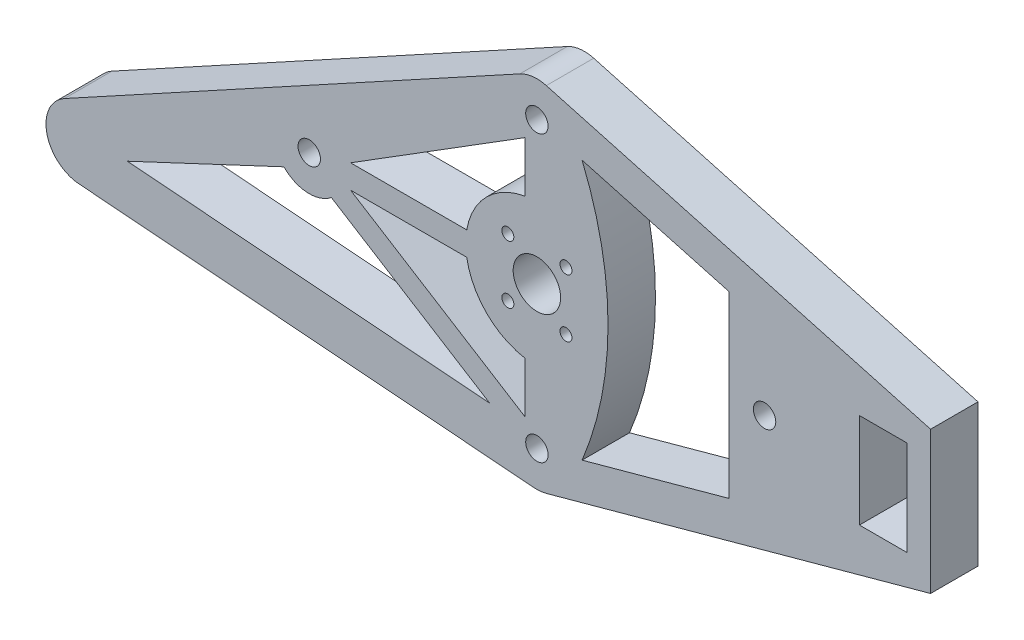
SolidWorks part; units mm, degrees
ref_plane "Front Plane" through (0, 0, 0) normal (0, 0, 1) x (1, 0, 0)
ref_plane "Top Plane" through (0, 0, 0) normal (0, 1, 0) x (1, 0, 0)
ref_plane "Right Plane" through (0, 0, 0) normal (1, 0, 0) x (0, 0, -1)
sketch "Sketch1" plane through (0, 0, 0) normal (0, 0, 1) x (1, 0, 0)
  line L0 (-3.8891, 3.8891) -> (3.8891, -3.8891) construction
  line L1 (0, -55) -> (0, 55) construction
  line L2 (-3.8891, -3.8891) -> (3.8891, 3.8891) construction
  line L3 (-1000, 0) -> (49000, 0) construction
  line L4 (-969.52, -25.4) -> (49030.48, -25.4) construction
  line L5 (40.005, 9.525) -> (52.705, 9.525) construction
  line L6 (43.18, 6.35) -> (49.53, 6.35)
  line L7 (43.18, 6.35) -> (43.18, -6.35)
  line L8 (43.18, -6.35) -> (49.53, -6.35)
  line L9 (49.53, 6.35) -> (49.53, -6.35)
  line L10 (43.18, 6.35) -> (49.53, -6.35) construction
  line L11 (43.18, -6.35) -> (49.53, 6.35) construction
  line L12 (52.705, 9.525) -> (52.705, -9.525)
  line L13 (40.005, -9.525) -> (52.705, -9.525) construction
  line L14 (40.005, 0) -> (40.005, -9.525) construction
  line L15 (55, 0) -> (-55, 0) construction
  line L16 (52.705, -9.525) -> (1.2604, -23.6427)
  line L17 (52.705, 9.525) -> (1.2604, 23.6427)
  line L18 (-61.3309, -19.0355) -> (-0.3709, -23.798)
  line L20 (-2.2851, 23.2285) -> (-63.2451, -10.109)
  line L21 (40.005, 9.525) -> (40.005, 0) construction
  line L22 (40.005, 9.525) -> (40.005, -9.525) construction
  line L23 (-63.2451, -10.109) -> (-91.2058, -25.4) construction
  circle A0 centre (0, 0) radius 3.175
  circle A1 centre (-3.8891, 3.8891) radius 0.8
  circle A2 centre (3.8891, -3.8891) radius 0.8
  circle A3 centre (30.48, 0) radius 1.5
  circle A4 centre (-30.48, 0) radius 1.5
  circle A5 centre (3.8891, 3.8891) radius 0.8
  circle A6 centre (-3.8891, -3.8891) radius 0.8
  circle A7 centre (30.48, 0) radius 25.4 construction
  circle A8 centre (-30.48, 0) radius 25.4 construction
  circle A9 centre (-60.96, -14.2875) radius 1.5 construction
  arc A10 (-63.2451, -10.109) -> (-61.3309, -19.0355) centre (-60.96, -14.2875) ccw
  circle A11 centre (0, -19.05) radius 1.5
  arc A12 (-0.3709, -23.798) -> (1.2604, -23.6427) centre (0, -19.05) ccw
  circle A13 centre (0, 19.05) radius 1.5
  arc A14 (-2.2851, 23.2285) -> (1.2604, 23.6427) centre (0, 19.05) cw
  arc A16 (-61.3309, -19.0355) -> (-63.2451, -10.109) centre (-60.96, -14.2875) ccw construction
  circle A17 centre (-28.8925, 15.875) radius 38.1 construction
  arc A20 (1.2604, 23.6427) -> (-2.2851, 23.2285) centre (0, 19.05) cw construction
  arc A21 (1.2604, -23.6427) -> (-0.3709, -23.798) centre (0, -19.05) ccw construction
  point P6 (0, 0)
  point P17 (0, 0)
  point P32 (0, -23.8125)
  point P33 (46.355, 0)
  point P50 (-92.3925, -25.4)
  point P51 (-28.8925, -22.225)
  point P52 (-66.9925, 15.875)
  point P57 (-51.8715, -3.8891)
  dimension "D1" = 6.35
  dimension "D3" = 3
  dimension "D4" = 1.6
  dimension "D7" = 50.8
  dimension "D10" = 9.525
  dimension "D11" = 1.5875
  dimension "D16" = 1.5875
  dimension "D18" = 76.2
  dimension "D2" = 11
  dimension "D5" = 45
  dimension "D6" = 30.48
  dimension "D8" = 11.1125
  dimension "D9" = 30.48
  dimension "D12" = 6.35
  dimension "D13" = 12.7
  dimension "D15" = 15.875
  dimension "D17" = 3.175
  dimension "D19" = 25.4
  dimension "D20" = 44.8319
  dimension "D14" = 3.175
extrude "Boss-Extrude1" add sketch "Sketch1" along normal mid plane 6.35
sketch "Sketch2" plane through (0, 0, 3.175) normal (0, 0, 1) x (1, 0, 0)
  line L0 (-60.96, -14.2875) -> (-30.48, 0) construction
  line L1 (-30.48, 0) -> (0, -19.05) construction
  line L2 (0, -19.05) -> (-60.96, -14.2875) construction
  line L3 (-6.3349, -16.9627) -> (-54.8423, -13.1731)
  line L4 (-54.8423, -13.1731) -> (-33.8718, -3.3432)
  line L5 (-27.5138, -3.726) -> (-6.3349, -16.9627)
  line L6 (-30.5886, -1.8042) -> (-27.5138, -3.726) construction
  line L7 (-30.5886, -1.8042) -> (-6.3349, -16.9627) construction
  line L8 (-33.8718, -3.3432) -> (-30.5886, -1.8042) construction
  line L9 (-54.8423, -13.1731) -> (-30.5886, -1.8042) construction
  line L10 (25.7175, 11.9925) -> (25.7175, -11.9925)
  line L11 (25.7175, 11.9925) -> (6.0495, 17.3899)
  line L12 (52.705, 9.525) -> (1.2604, 23.6427) construction
  line L13 (25.7175, -11.9925) -> (6.0495, -17.3899)
  line L14 (1.2604, -23.6427) -> (52.705, -9.525) construction
  arc A0 (-33.8718, -3.3432) -> (-27.5138, -3.726) centre (-30.48, 0) ccw
  circle A1 centre (0, -19.05) radius 4.7625 construction
  circle A2 centre (-60.96, -14.2875) radius 4.7625 construction
  circle A3 centre (0, 0) radius 9.525 construction
  circle A4 centre (0, 19.05) radius 4.7625 construction
  circle A5 centre (30.48, 0) radius 4.7625 construction
  arc A6 (-26.4414, -2.5241) -> (-34.7922, -2.0214) centre (-30.48, 0) ccw construction
  arc A7 (-34.7922, -2.0214) -> (-33.8718, -3.3432) centre (-30.48, 0) ccw construction
  arc A8 (-27.5138, -3.726) -> (-26.4414, -2.5241) centre (-30.48, 0) ccw construction
  arc A9 (6.0495, 17.3899) -> (6.0495, -17.3899) centre (-35.7188, 0) cw
  arc A10 (4.2022, 21.2912) -> (6.0495, 17.3899) centre (-35.7188, 0) cw construction
  arc A11 (6.0495, -17.3899) -> (4.2022, -21.2912) centre (-35.7188, 0) cw construction
  arc A13 (-63.2451, -10.109) -> (-61.3309, -19.0355) centre (-60.96, -14.2875) ccw construction
  point P30 (25.7175, 0)
  point P36 (-60.96, -14.2875)
  point P37 (-59.4621, -15.7011)
  dimension "D1" = 9.525
  dimension "D2" = 19.05
  dimension "D4" = 4.7625
  dimension "D3" = 1.5875
extrude "Cut-Extrude1" cut sketch "Sketch2" against normal through all
sketch "Sketch3" plane through (0, 0, 3.175) normal (0, 0, 1) x (1, 0, 0)
  line L0 (-30.48, 0) -> (0, 0) construction
  line L1 (0, 0) -> (0, -19.05) construction
  line L2 (0, -19.05) -> (-30.48, 0) construction
  line L3 (-1.5875, -16.1858) -> (-24.9447, -1.5875)
  line L4 (-24.9447, -1.5875) -> (-9.3918, -1.5875)
  line L5 (-1.5875, -9.3918) -> (-1.5875, -16.1858)
  line L6 (-9.3918, -1.5875) -> (-1.5875, -1.5875) construction
  line L7 (-24.9447, -1.5875) -> (-1.5875, -1.5875) construction
  line L8 (-1.5875, -1.5875) -> (-1.5875, -9.3918) construction
  line L9 (-1.5875, -1.5875) -> (-1.5875, -16.1858) construction
  arc A0 (-9.3918, -1.5875) -> (-1.5875, -9.3918) centre (0, 0) ccw
  arc A1 (0, -9.525) -> (-9.525, 0) centre (0, 0) ccw construction
  arc A2 (-9.525, 0) -> (-9.3918, -1.5875) centre (0, 0) ccw construction
  arc A3 (-1.5875, -9.3918) -> (0, -9.525) centre (0, 0) ccw construction
  dimension "D1" = 19.05
  dimension "D2" = 1.5875
extrude "Cut-Extrude2" cut sketch "Sketch3" against normal through all
mirror "Mirror1" about plane through (0, 0, 0) normal (0, 1, 0) of "Cut-Extrude2"
